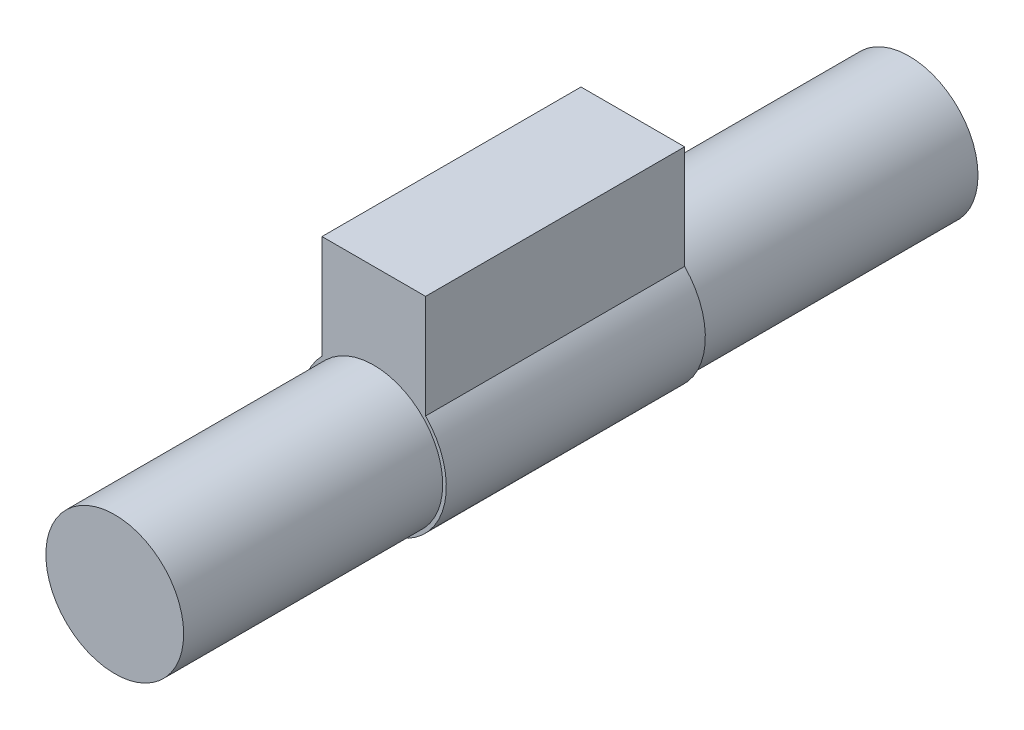
SolidWorks part; units mm, degrees
ref_plane "Front Plane" through (0, 0, 0) normal (0, 0, 1) x (1, 0, 0)
ref_plane "Top Plane" through (0, 0, 0) normal (0, 1, 0) x (1, 0, 0)
ref_plane "Right Plane" through (0, 0, 0) normal (1, 0, 0) x (0, 0, -1)
sketch "Sketch1" plane through (0, 0, 0) normal (0, 0, 1) x (1, 0, 0)
  circle A0 centre (-14.3839, -0.8549) radius 3.99
  dimension "D1" = 7.98
extrude "Boss-Extrude1" add sketch "Sketch1" along normal blind 16
sketch "Sketch6" plane through (0, 0, 16) normal (0, 0, 1) x (1, 0, 0)
  line L2 (-17.3839, 2.0845) -> (-17.3839, 8.0845)
  line L3 (-17.3839, 8.0845) -> (-11.3839, 8.0845)
  line L4 (-11.3839, 2.0845) -> (-11.3839, 8.0845)
  arc A0 (-17.3839, 2.0845) -> (-11.3839, 2.0845) centre (-14.3839, -0.8549) ccw
  circle A1 centre (-14.3839, -0.8549) radius 3.99 construction
  dimension "D1" = 0
  dimension "D5" = 6
  dimension "D6" = 6
extrude "Boss-Extrude7" add sketch "Sketch6" along normal blind 15
sketch "Sketch7" plane through (0, 0, 31) normal (0, 0, 1) x (1, 0, 0)
  circle A0 centre (-14.3839, -0.8549) radius 3.99
  arc A1 (-17.3839, 2.0845) -> (-11.3839, 2.0845) centre (-14.3839, -0.8549) ccw construction
  dimension "D1" = 0
  dimension "D2" = 7.98
extrude "Boss-Extrude8" add sketch "Sketch7" along normal blind 15
